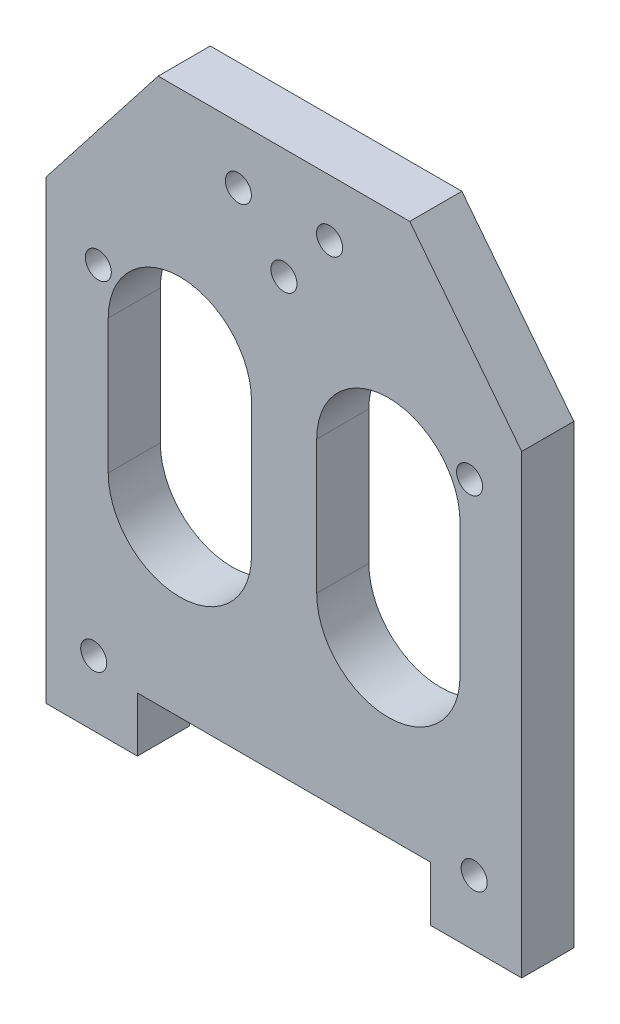
SolidWorks part; units mm, degrees
ref_plane "Plano frontal" through (0, 0, 0) normal (0, 0, 1) x (1, 0, 0)
ref_plane "Plano superior" through (0, 0, 0) normal (0, 1, 0) x (1, 0, 0)
ref_plane "Plano direito" through (0, 0, 0) normal (1, 0, 0) x (0, 0, -1)
sketch "Esboço2" plane through (0, 0, 0) normal (0, 0, 1) x (1, 0, 0)
  line L0 (0.0227, -19.0097) -> (16.0302, -19.0875) construction
  line L1 (0.0227, -19.0097) -> (-15.9774, -19.0097) construction
  line L2 (0.0473, -39.5911) -> (16.0302, -39.5911) construction
  line L3 (0.0898, -75.138) -> (-0.0199, 16.6193) construction
  line L4 (0.0473, -39.5911) -> (-15.9774, -39.5911) construction
  line L5 (27.0302, -19.0875) -> (27.0302, -39.5911)
  line L6 (5.0302, -19.0875) -> (5.0302, -39.5911)
  line L7 (-4.9774, -39.5911) -> (-4.9774, -19.0097)
  line L8 (-26.9774, -19.0097) -> (-26.9774, -39.5911)
  line L20 (19.3117, 17) -> (-19.3117, 17)
  line L21 (-19.3117, 17) -> (-36.5, -5)
  line L22 (-36.5, -5) -> (-36.5, -75)
  line L23 (-36.5, -75) -> (-22.5, -75)
  line L24 (-22.5, -75) -> (-22.5, -66.6)
  line L25 (-22.5, -66.6) -> (22.5, -66.6)
  line L26 (22.5, -66.6) -> (22.5, -75)
  line L27 (22.5, -75) -> (36.5, -75)
  line L28 (36.5, -75) -> (36.5, -5)
  line L29 (36.5, -5) -> (19.3117, 17)
  arc A0 (-4.9774, -19.0097) -> (-26.9774, -19.0097) centre (-15.9774, -19.0097) ccw
  arc A1 (27.0302, -19.0875) -> (5.0302, -19.0875) centre (16.0302, -19.0875) ccw
  arc A2 (-26.9774, -39.5911) -> (-4.9774, -39.5911) centre (-15.9774, -39.5911) ccw
  arc A3 (5.0302, -39.5911) -> (27.0302, -39.5911) centre (16.0302, -39.5911) ccw
  circle A13 centre (0, 0) radius 2
  circle A14 centre (-7, 8.3) radius 2
  circle A15 centre (7, 8.3) radius 2
  circle A16 centre (-28.5, -12.7) radius 2
  circle A20 centre (-29.2, -65) radius 2
  circle A21 centre (29.2, -65) radius 2
  circle A25 centre (28.5, -12.7) radius 2
  point P17 (0, 0)
extrude "Ressalto-extrusão1" add sketch "Esboço2" along normal blind 8 contours L28 L29 L20 L21 L22 L23 L24 L25 L26 L27 A25 A21 A20 A16 A15 A14 A13 A3 L6 A1 L5 A2 L8 A0 L7
